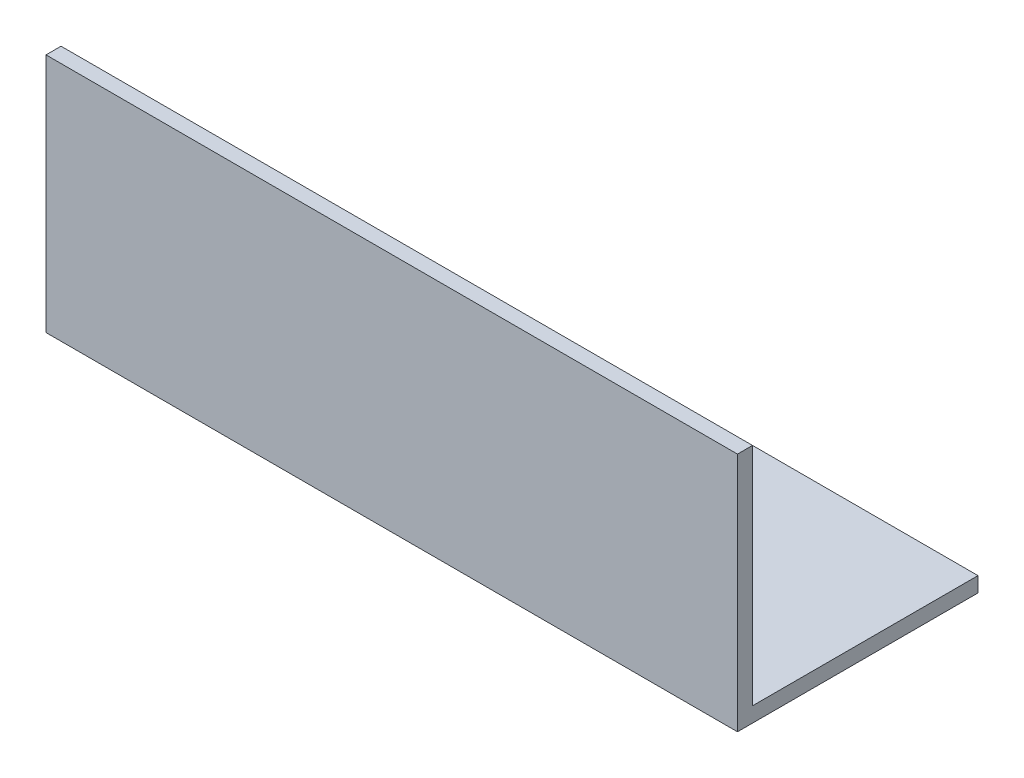
SolidWorks part; units mm, degrees
ref_plane "Спереди" through (0, 0, 0) normal (0, 0, 1) x (1, 0, 0)
ref_plane "Сверху" through (0, 0, 0) normal (0, 1, 0) x (1, 0, 0)
ref_plane "Справа" through (0, 0, 0) normal (1, 0, 0) x (0, 0, -1)
sketch "Эскиз1" plane through (0, 0, 0) normal (1, 0, 0) x (0, 0, -1)
  line L0 (0, 0) -> (0, 75)
  line L1 (0, 0) -> (75, 0)
extrude "Вытянуть-Тонкостенный1" add sketch "Эскиз1" along normal blind 230 thin thin type one direction wall 5
